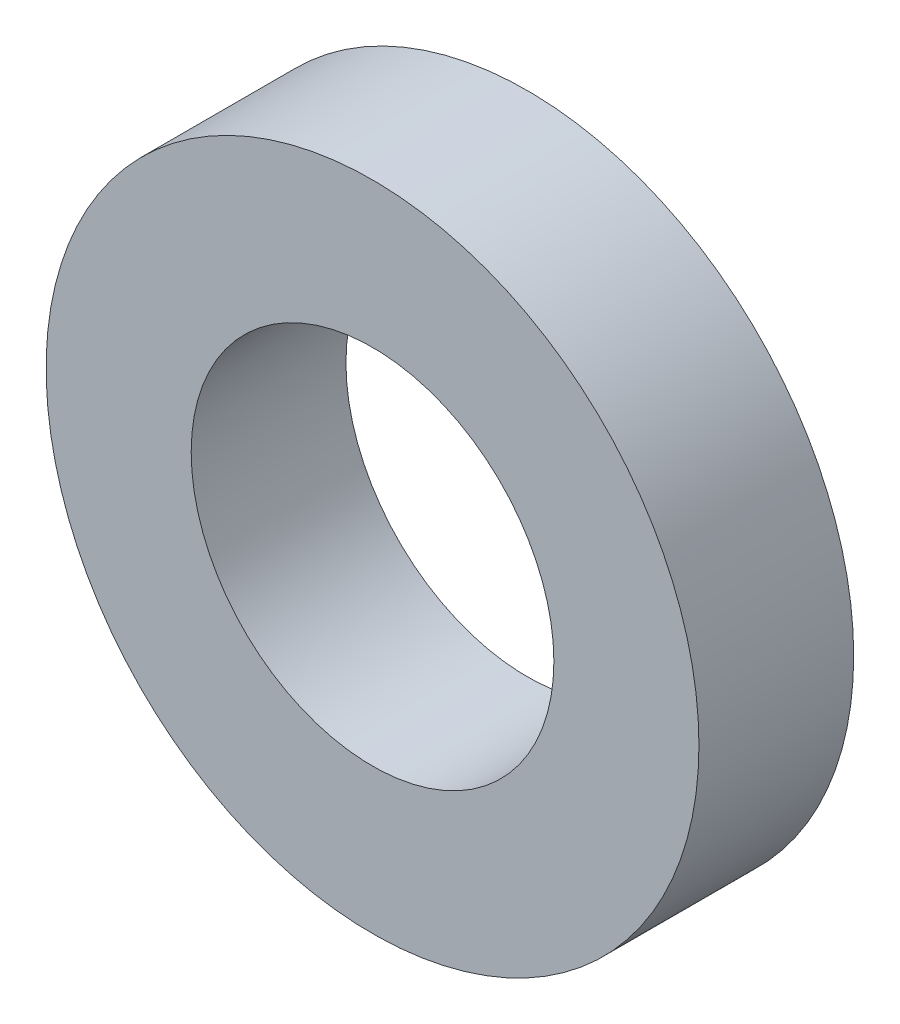
SolidWorks part; units mm, degrees
ref_plane "Alzado" through (0, 0, 0) normal (0, 0, 1) x (1, 0, 0)
ref_plane "Planta" through (0, 0, 0) normal (0, 1, 0) x (1, 0, 0)
ref_plane "Vista lateral" through (0, 0, 0) normal (1, 0, 0) x (0, 0, -1)
sketch "Croquis1" plane through (0, 0, 0) normal (0, 0, 1) x (1, 0, 0)
  circle A0 centre (0, 0) radius 3.75
  circle A1 centre (0, 0) radius 6.75
  dimension "D1" = 7.5
  dimension "D2" = 3
extrude "Saliente-Extruir1" add sketch "Croquis1" along normal blind 3.2
